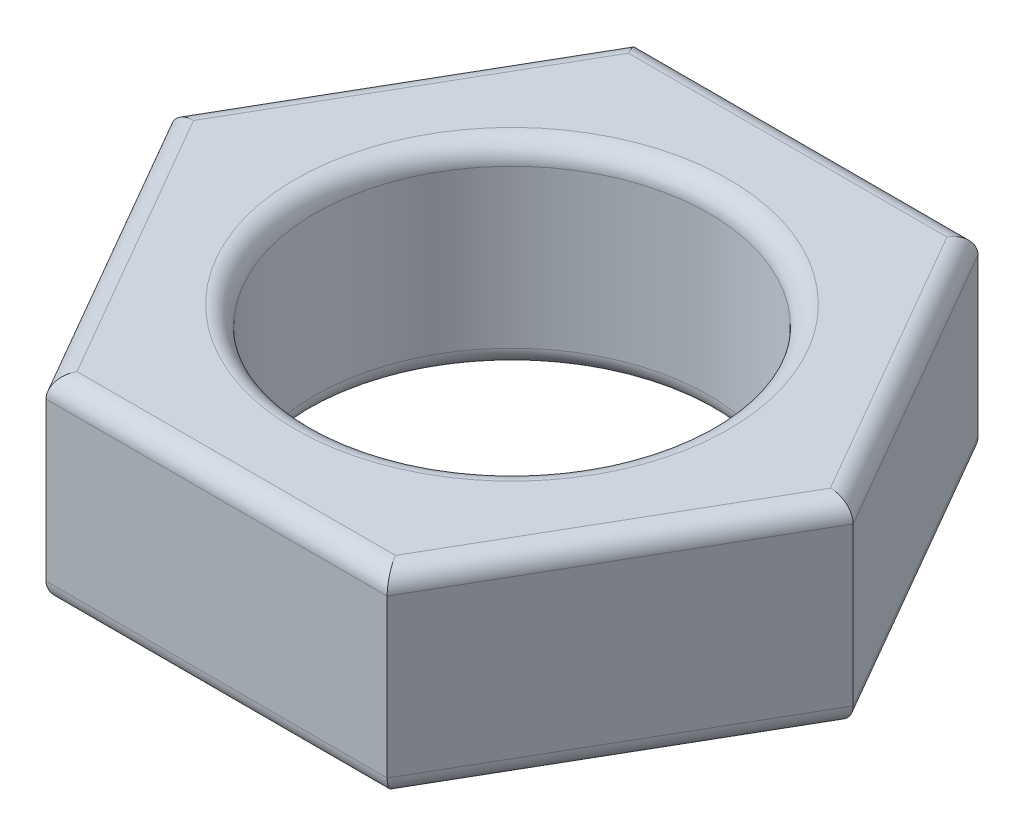
SolidWorks part; units mm, degrees
ref_plane "Front Plane" through (0, 0, 0) normal (0, 0, 1) x (1, 0, 0)
ref_plane "Top Plane" through (0, 0, 0) normal (0, 1, 0) x (1, 0, 0)
ref_plane "Right Plane" through (0, 0, 0) normal (1, 0, 0) x (0, 0, -1)
sketch "Sketch1" plane through (0, 0, 0) normal (0, 1, 0) x (1, 0, 0)
  line L1 (4.3301, -7.5) -> (8.6603, 0)
  line L2 (8.6603, 0) -> (4.3301, 7.5)
  line L3 (4.3301, 7.5) -> (-4.3301, 7.5)
  line L4 (-4.3301, 7.5) -> (-8.6603, 0)
  line L5 (-8.6603, 0) -> (-4.3301, -7.5)
  line L6 (-4.3301, -7.5) -> (4.3301, -7.5)
  circle A0 centre (0, 0) radius 7.5 construction
  circle A1 centre (0, 0) radius 5
  dimension "D1" = 15
  dimension "D2" = 10
extrude "Boss-Extrude1" add sketch "Sketch1" along normal blind 5
fillet "Fillet1" radius 0.5 14 edges at (0, 0, 5) (6.4952, 0, 3.75) (6.4952, 0, -3.75) (0, 0, -7.5) (-6.4952, 0, -3.75) (-6.4952, 0, 3.75) (0, 0, 7.5) (0, 5, 5) (-6.4952, 5, 3.75) (-6.4952, 5, -3.75) (0, 5, -7.5) (6.4952, 5, -3.75) (6.4952, 5, 3.75) (0, 5, 7.5)
